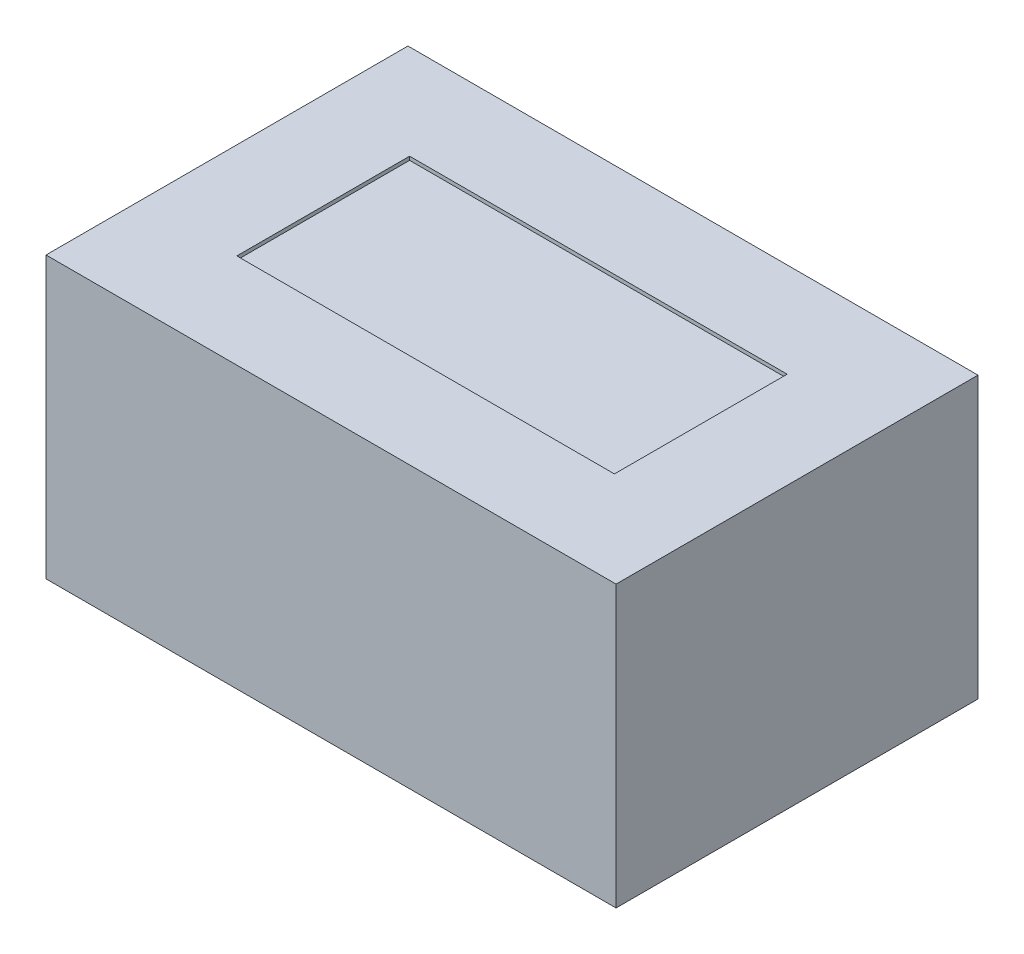
SolidWorks part; units mm, degrees
ref_plane "Alzado" through (0, 0, 0) normal (0, 0, 1) x (1, 0, 0)
ref_plane "Planta" through (0, 0, 0) normal (0, 1, 0) x (1, 0, 0)
ref_plane "Vista lateral" through (0, 0, 0) normal (1, 0, 0) x (0, 0, -1)
sketch "Croquis1" plane through (0, 0, 0) normal (0, 1, 0) x (1, 0, 0)
  line L1 (-157.5, -100) -> (157.5, -100)
  line L2 (-157.5, -100) -> (-157.5, 100)
  line L3 (-157.5, 100) -> (157.5, 100)
  line L4 (157.5, -100) -> (157.5, 100)
  line L5 (-157.5, -100) -> (157.5, 100) construction
  line L6 (-157.5, 100) -> (157.5, -100) construction
  point P0 (0, 0)
  dimension "D1" = 315
  dimension "D2" = 200
extrude "Saliente-Extruir1" add sketch "Croquis1" along normal blind 155
sketch "Croquis2" plane through (0, 155, 0) normal (0, 1, 0) x (1, 0, 0)
  line L1 (-104.3244, -47.7333) -> (104.3244, -47.7333)
  line L2 (-104.3244, -47.7333) -> (-104.3244, 47.7333)
  line L3 (-104.3244, 47.7333) -> (104.3244, 47.7333)
  line L4 (104.3244, -47.7333) -> (104.3244, 47.7333)
  line L5 (-104.3244, -47.7333) -> (104.3244, 47.7333) construction
  line L6 (-104.3244, 47.7333) -> (104.3244, -47.7333) construction
  point P0 (0, 0)
extrude "Cortar-Extruir1" cut sketch "Croquis2" against normal blind 2
